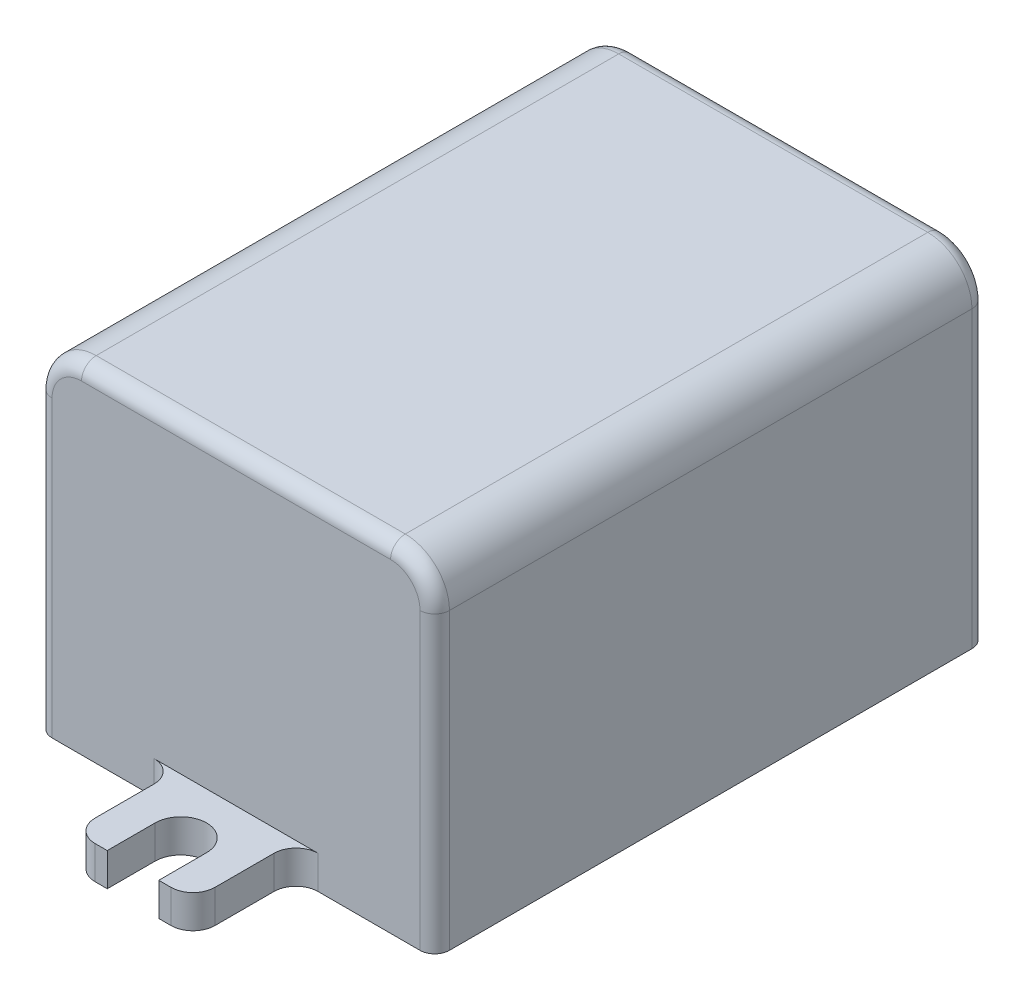
SolidWorks part; units mm, degrees
material "ABS"
ref_plane "Front Plane" through (0, 0, 0) normal (0, 0, 1) x (1, 0, 0)
ref_plane "Top Plane" through (0, 0, 0) normal (0, 1, 0) x (1, 0, 0)
ref_plane "Right Plane" through (0, 0, 0) normal (1, 0, 0) x (0, 0, -1)
sketch "Sketch1" plane through (0, 0, 0) normal (0, 1, 0) x (1, 0, 0)
  line L1 (13.5, -18.75) -> (-13.5, -18.75)
  line L2 (13.5, -18.75) -> (13.5, 18.75)
  line L3 (13.5, 18.75) -> (-13.5, 18.75)
  line L4 (-13.5, -18.75) -> (-13.5, 18.75)
  line L5 (13.5, -18.75) -> (-13.5, 18.75) construction
  line L6 (13.5, 18.75) -> (-13.5, -18.75) construction
  point P0 (0, 0)
  dimension "D1" = 27
  dimension "D2" = 37.5
extrude "Boss-Extrude1" add sketch "Sketch1" along normal blind 23
sketch "Sketch2" plane through (0, 0, 0) normal (0, 1, 0) x (1, 0, 0)
  line L0 (0, -28.9672) -> (0, 24.8229) construction
  line L1 (-21.2397, 0) -> (21.6714, 0) construction
  line L2 (-1.75, -22.5) -> (-1.75, -25.75)
  line L3 (-1.75, -25.75) -> (-2.575, -25.75)
  line L4 (-4.075, -24.25) -> (-4.075, -20.25)
  line L5 (-13.5, -18.75) -> (13.5, -18.75) construction
  line L6 (-5.575, -18.75) -> (5.575, -18.75)
  line L7 (4.075, -24.25) -> (4.075, -20.25)
  line L8 (1.75, -25.75) -> (2.575, -25.75)
  line L9 (1.75, -22.5) -> (1.75, -25.75)
  line L10 (1.75, 22.5) -> (1.75, 25.75)
  line L11 (1.75, 25.75) -> (2.575, 25.75)
  line L12 (4.075, 24.25) -> (4.075, 20.25)
  line L13 (-5.575, 18.75) -> (5.575, 18.75)
  line L14 (-4.075, 24.25) -> (-4.075, 20.25)
  line L15 (-1.75, 25.75) -> (-2.575, 25.75)
  line L16 (-1.75, 22.5) -> (-1.75, 25.75)
  arc A0 (-1.75, -22.5) -> (1.75, -22.5) centre (0, -22.5) cw
  arc A1 (-4.075, -20.25) -> (-5.575, -18.75) centre (-5.575, -20.25) ccw
  arc A2 (-2.575, -25.75) -> (-4.075, -24.25) centre (-2.575, -24.25) cw
  arc A3 (2.575, -25.75) -> (4.075, -24.25) centre (2.575, -24.25) ccw
  arc A4 (4.075, -20.25) -> (5.575, -18.75) centre (5.575, -20.25) cw
  arc A5 (4.075, 20.25) -> (5.575, 18.75) centre (5.575, 20.25) ccw
  arc A6 (2.575, 25.75) -> (4.075, 24.25) centre (2.575, 24.25) cw
  arc A7 (-2.575, 25.75) -> (-4.075, 24.25) centre (-2.575, 24.25) ccw
  arc A8 (-4.075, 20.25) -> (-5.575, 18.75) centre (-5.575, 20.25) cw
  arc A9 (-1.75, 22.5) -> (1.75, 22.5) centre (0, 22.5) ccw
  point P17 (0, -18.75)
  point P25 (0, -22.2218)
  point P26 (0, -20.75)
  point P44 (0, 18.75)
  dimension "D1" = 1.5
  dimension "D2" = 1.5
  dimension "D3" = 8.15
  dimension "D4" = 7
  dimension "D5" = 5
  dimension "D6" = 3.5
extrude "Boss-Extrude2" add sketch "Sketch2" along normal blind 2.25
fillet "Fillet1" radius 3 2 edges at (13.5, 23, 0) (-13.5, 23, 0)
fillet "Fillet2" radius 1 10 edges at (13.5, 10, 18.75) (12.6213, 22.1213, 18.75) (0, 23, 18.75) (-12.6213, 22.1213, 18.75) (13.5, 10, -18.75) (12.6213, 22.1213, -18.75) (0, 23, -18.75) (-12.6213, 22.1213, -18.75) (-13.5, 10, 18.75) (-13.5, 10, -18.75)
